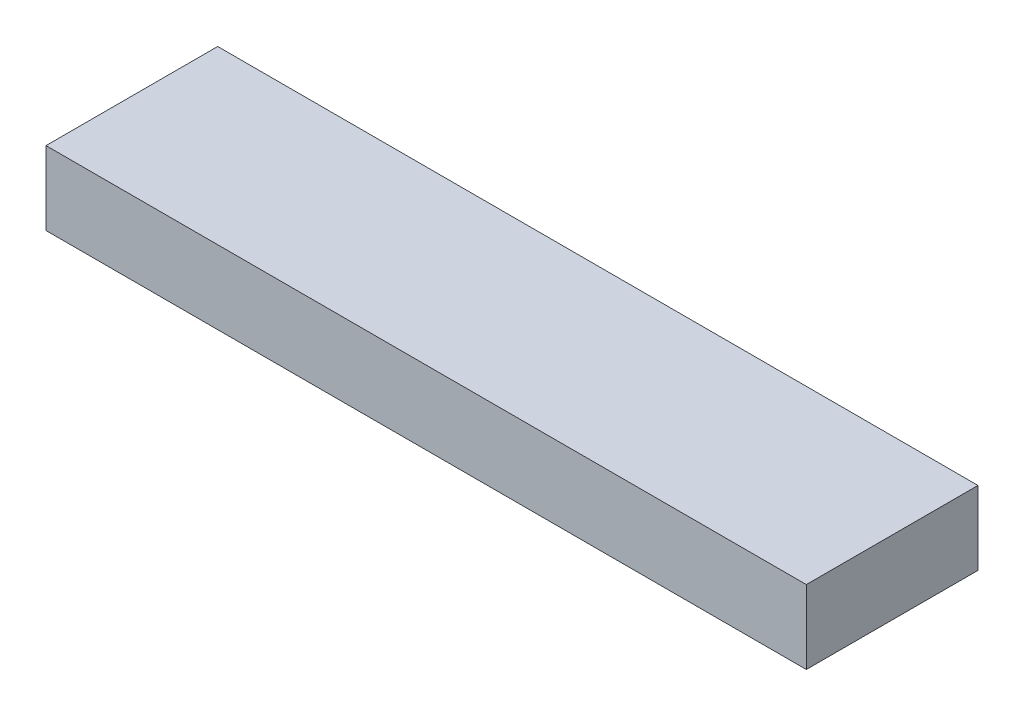
SolidWorks part; units mm, degrees
ref_plane "Front Plane" through (0, 0, 0) normal (0, 0, 1) x (1, 0, 0)
ref_plane "Top Plane" through (0, 0, 0) normal (0, 1, 0) x (1, 0, 0)
ref_plane "Right Plane" through (0, 0, 0) normal (1, 0, 0) x (0, 0, -1)
sketch "Sketch1" plane through (0, 0, 0) normal (0, 1, 0) x (1, 0, 0)
  line L1 (0, 0) -> (393.7, 0)
  line L2 (0, 0) -> (0, 88.9)
  line L3 (0, 88.9) -> (393.7, 88.9)
  line L4 (393.7, 0) -> (393.7, 88.9)
  dimension "D1" = 88.9
  dimension "D2" = 393.7
extrude "Boss-Extrude1" add sketch "Sketch1" along normal blind 38.1
